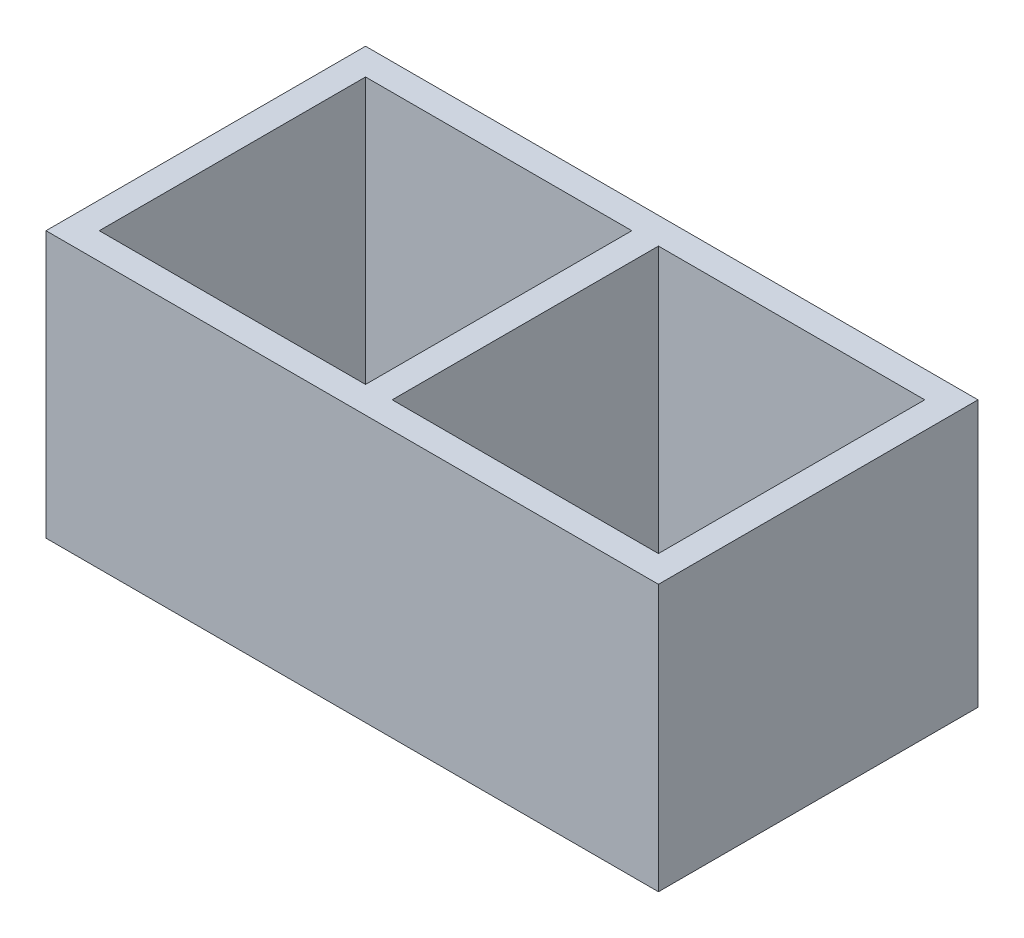
SolidWorks part; units mm, degrees
ref_plane "Front Plane" through (0, 0, 0) normal (0, 0, 1) x (1, 0, 0)
ref_plane "Top Plane" through (0, 0, 0) normal (0, 1, 0) x (1, 0, 0)
ref_plane "Right Plane" through (0, 0, 0) normal (1, 0, 0) x (0, 0, -1)
sketch "Sketch1" plane through (0, 0, 0) normal (0, 1, 0) x (1, 0, 0)
  line L0 (-0.75, 0) -> (0, 0) construction
  line L1 (17.25, -9) -> (-17.25, -9)
  line L2 (17.25, -9) -> (17.25, 9)
  line L3 (17.25, 9) -> (-17.25, 9)
  line L4 (-17.25, -9) -> (-17.25, 9)
  line L5 (17.25, -9) -> (-17.25, 9) construction
  line L6 (17.25, 9) -> (-17.25, -9) construction
  line L7 (-15.75, -7.5) -> (-0.75, -7.5)
  line L8 (-15.75, -7.5) -> (-15.75, 7.5)
  line L9 (-15.75, 7.5) -> (-0.75, 7.5)
  line L10 (-0.75, -7.5) -> (-0.75, 7.5)
  line L11 (-15.75, -7.5) -> (-0.75, 7.5) construction
  line L12 (-15.75, 7.5) -> (-0.75, -7.5) construction
  line L13 (15.75, -7.5) -> (0.75, -7.5)
  line L14 (15.75, -7.5) -> (15.75, 7.5)
  line L15 (15.75, 7.5) -> (0.75, 7.5)
  line L16 (0.75, -7.5) -> (0.75, 7.5)
  line L17 (15.75, -7.5) -> (0.75, 7.5) construction
  line L18 (15.75, 7.5) -> (0.75, -7.5) construction
  line L19 (0, 0) -> (0.75, 0) construction
  point P0 (0, 0)
  point P6 (-8.25, 0)
  point P11 (8.25, 0)
  dimension "D1" = 15
  dimension "D2" = 1.5
  dimension "D3" = 1.5
  dimension "D4" = 15
  dimension "D5" = 18
extrude "Boss-Extrude1" add sketch "Sketch1" along normal blind 15
